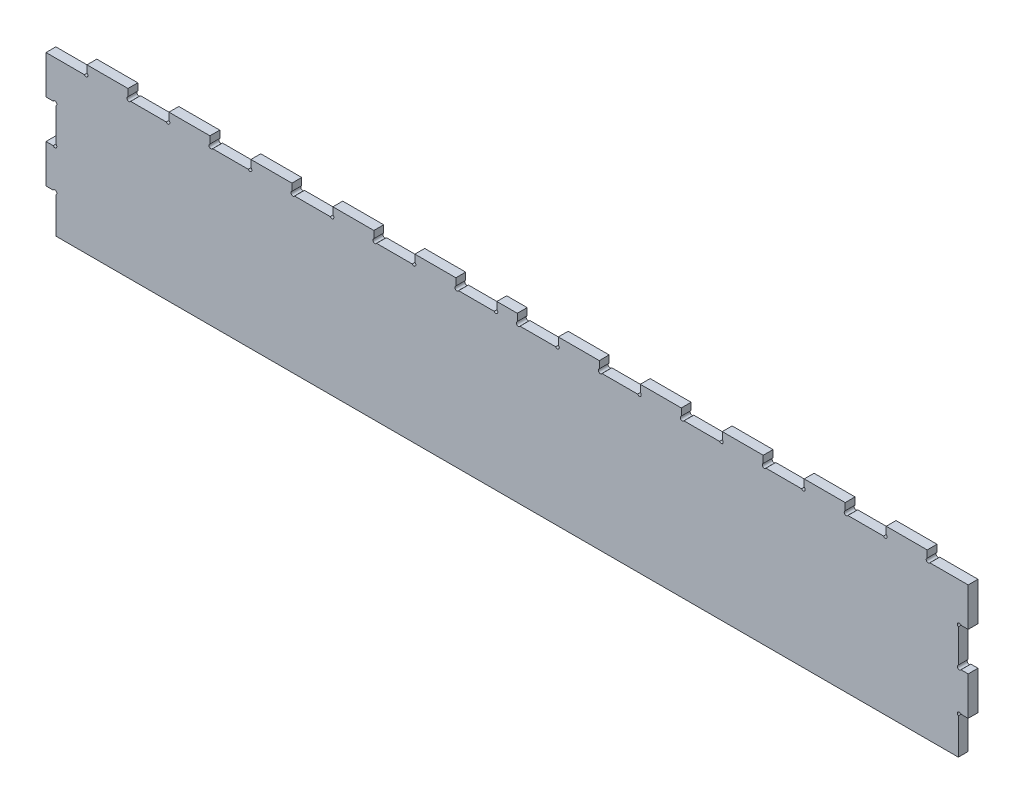
SolidWorks part; units mm, degrees
ref_plane "Front Plane" through (0, 0, 0) normal (0, 0, 1) x (1, 0, 0)
ref_plane "Top Plane" through (0, 0, 0) normal (0, 1, 0) x (1, 0, 0)
ref_plane "Right Plane" through (0, 0, 0) normal (1, 0, 0) x (0, 0, -1)
sketch "Sketch1" plane through (0, 0, 0) normal (0, 0, 1) x (1, 0, 0)
  line L0 (-398.4815, 104.8969) -> (-351.7791, 104.8969)
  line L1 (-348.4815, 116.8969) -> (-298.4815, 116.8969)
  line L2 (-398.4815, 104.8969) -> (-398.4815, 57.8969)
  line L3 (-386.4815, -83.1031) -> (714.5185, -83.1031)
  line L4 (726.5185, 104.8969) -> (726.5185, 57.8969)
  line L5 (-348.4815, 108.1642) -> (-348.4815, 116.8969)
  line L6 (-298.4815, 116.8969) -> (-298.4815, 108.1642)
  line L7 (-295.1839, 104.8969) -> (-251.7791, 104.8969)
  line L8 (-248.4815, 108.1642) -> (-248.4815, 116.8969)
  line L9 (-248.4815, 116.8969) -> (-198.4815, 116.8969)
  line L10 (-198.4815, 116.8969) -> (-198.4815, 108.1642)
  line L11 (-195.1839, 104.8969) -> (-151.7791, 104.8969)
  line L12 (-148.4815, 108.1642) -> (-148.4815, 116.8969)
  line L13 (-148.4815, 116.8969) -> (-98.4815, 116.8969)
  line L14 (-98.4815, 116.8969) -> (-98.4815, 108.1642)
  line L15 (-95.1839, 104.8969) -> (-51.7791, 104.8969)
  line L16 (426.5185, 108.1642) -> (426.5185, 116.8969)
  line L17 (426.5185, 116.8969) -> (476.5185, 116.8969)
  line L18 (-348.4815, 104.8969) -> (-348.4815, 107.2969) construction
  line L19 (-348.4815, 107.2969) -> (-348.4815, 106.0969) construction
  line L20 (-348.4815, 104.8969) -> (-348.4815, 107.2969) construction
  line L21 (-348.4815, 107.2969) -> (-348.4815, 106.0969) construction
  line L22 (-348.4815, 106.0969) -> (-454.6532, 106.0969) construction
  line L23 (-454.6532, 106.0969) -> (-401.5674, 106.0969) construction
  line L24 (-348.4815, 112.5305) -> (-298.4815, 112.5305) construction
  line L25 (-348.4815, 104.8969) -> (-349.7007, 104.8969) construction
  line L26 (-350.9198, 104.8969) -> (-349.7007, 104.8969) construction
  line L27 (-349.7007, 104.8969) -> (-349.7007, 106.4267) construction
  line L28 (-350.8815, 104.8969) -> (-350.9198, 104.8969) construction
  line L29 (-298.4815, 112.5305) -> (-323.4815, 112.5305) construction
  line L30 (-323.4815, 112.5305) -> (-323.4815, 101.2566) construction
  line L31 (-298.4815, 112.5305) -> (-248.4815, 112.5305) construction
  line L32 (-248.4815, 112.5305) -> (-273.4815, 112.5305) construction
  line L33 (-273.4815, 112.5305) -> (-273.4815, 99.7895) construction
  line L34 (-248.4815, 113.8454) -> (-198.4815, 113.8454) construction
  line L35 (-198.4815, 113.8454) -> (-223.4815, 113.8454) construction
  line L36 (-223.4815, 113.8454) -> (-223.4815, 90.9782) construction
  line L37 (-198.4815, 112.5305) -> (-148.4815, 112.5305) construction
  line L38 (-148.4815, 112.5305) -> (-173.4815, 112.5305) construction
  line L39 (-173.4815, 112.5305) -> (-173.4815, 98.0011) construction
  line L40 (-148.4815, 109.9027) -> (-98.4815, 109.9027) construction
  line L41 (-98.4815, 109.9027) -> (-123.4815, 109.9027) construction
  line L42 (-123.4815, 109.9027) -> (-123.4815, 98.0011) construction
  line L43 (651.5185, 116.8969) -> (651.5185, -83.1031) construction
  line L44 (651.5185, -83.1031) -> (651.5185, 16.8969) construction
  line L45 (164.0185, 10.8969) -> (164.0185, 307.3359) construction
  line L46 (426.5185, 116.8969) -> (426.5185, 108.1642)
  line L47 (476.5185, 108.1642) -> (476.5185, 116.8969)
  line L48 (523.2209, 104.8969) -> (479.8161, 104.8969)
  line L49 (526.5185, 116.8969) -> (526.5185, 108.1642)
  line L50 (576.5185, 108.1642) -> (576.5185, 116.8969)
  line L51 (623.2209, 104.8969) -> (579.8161, 104.8969)
  line L52 (626.5185, 116.8969) -> (626.5185, 108.1642)
  line L53 (676.5185, 108.1642) -> (676.5185, 116.8969)
  line L54 (726.5185, 104.8969) -> (679.8161, 104.8969)
  line L55 (526.5185, 116.8969) -> (576.5185, 116.8969)
  line L56 (626.5185, 116.8969) -> (676.5185, 116.8969)
  line L57 (651.5185, 16.8969) -> (-398.4815, 16.8969) construction
  line L58 (726.5185, 10.8969) -> (726.5185, -36.1031)
  line L59 (-388.8815, 57.8969) -> (-388.8748, 57.8969)
  line L60 (-386.4815, 57.8969) -> (-388.8748, 57.8969) construction
  line L61 (-388.8748, 57.8969) -> (-387.6782, 57.8969) construction
  line L62 (-387.6782, 57.8969) -> (-387.6782, 56.1544) construction
  line L63 (-386.4815, 57.8969) -> (-386.4815, 55.4969) construction
  line L64 (-386.4815, 55.4969) -> (-386.4815, 56.6969) construction
  line L65 (-386.4815, 56.6969) -> (-387.892, 56.6969) construction
  line L66 (-386.4815, 54.6165) -> (-386.4815, 14.1773)
  line L67 (714.5185, -71.1031) -> (714.5185, -83.1031)
  line L68 (714.5185, -39.3835) -> (714.5185, -71.1031)
  line L69 (726.5185, -36.1031) -> (717.7936, -36.1031)
  line L70 (717.7936, 10.8969) -> (726.5185, 10.8969)
  line L71 (714.5185, 54.6165) -> (714.5185, 14.1773)
  line L72 (726.5185, 57.8969) -> (717.7936, 57.8969)
  line L73 (-386.4815, -39.3835) -> (-386.4815, -83.1031)
  line L74 (376.5185, 108.1642) -> (376.5185, 116.8969)
  line L75 (376.5185, 116.8969) -> (326.5185, 116.8969)
  line L76 (326.5185, 116.8969) -> (326.5185, 108.1642)
  line L77 (379.8161, 104.8969) -> (423.2209, 104.8969)
  line L78 (276.5185, 108.1642) -> (276.5185, 116.8969)
  line L79 (276.5185, 116.8969) -> (226.5185, 116.8969)
  line L80 (226.5185, 116.8969) -> (226.5185, 108.1642)
  line L81 (279.8161, 104.8969) -> (323.2209, 104.8969)
  line L82 (176.5185, 108.1642) -> (176.5185, 116.8969)
  line L83 (-398.4815, 57.8969) -> (-389.7566, 57.8969)
  line L84 (-398.4815, 57.8969) -> (-398.4815, 10.8969) construction
  line L85 (-389.7566, 10.8969) -> (-398.4815, 10.8969)
  line L86 (-398.4815, 10.8969) -> (-398.4815, -36.1031)
  line L87 (-398.4815, -36.1031) -> (-389.7566, -36.1031)
  line L88 (176.5185, 116.8969) -> (151.5185, 116.8969)
  line L89 (151.5185, 116.8969) -> (151.5185, 108.1642)
  line L90 (179.8161, 104.8969) -> (223.2209, 104.8969)
  line L91 (376.5185, 116.8969) -> (426.5185, 116.8969) construction
  line L92 (-386.4815, 55.4969) -> (-386.4815, 57.8969) construction
  line L93 (351.5185, 116.8969) -> (351.5185, 66.1173) construction
  line L94 (301.5185, 104.8969) -> (301.5185, 57.8969) construction
  line L95 (-398.4815, 34.3969) -> (-378.9007, 34.3969) construction
  line L96 (-398.4815, -12.6031) -> (-375.299, -12.6031) construction
  line L97 (251.5185, 116.8969) -> (251.5185, 57.8969) construction
  line L98 (201.5185, 104.8969) -> (201.5185, 57.8969) construction
  line L99 (401.5185, 116.8969) -> (401.5185, 79.0498) construction
  line L100 (-48.4815, 108.1642) -> (-48.4815, 116.8969)
  line L101 (-48.4815, 116.8969) -> (1.5185, 116.8969)
  line L102 (51.5185, 116.8969) -> (101.5185, 116.8969)
  line L103 (1.5185, 116.8969) -> (1.5185, 108.1642)
  line L105 (51.5185, 108.1642) -> (51.5185, 116.8969)
  line L106 (101.5185, 116.8969) -> (101.5185, 108.1642)
  line L107 (104.8161, 104.8969) -> (148.2209, 104.8969)
  line L108 (4.8161, 104.8969) -> (48.2209, 104.8969)
  circle A0 centre (-348.4815, 104.8969) radius 2.4 construction
  arc A1 (-351.7791, 104.8969) -> (-348.4815, 108.1642) centre (-349.7007, 106.0969) ccw
  arc A2 (-295.1839, 104.8969) -> (-298.4815, 108.1642) centre (-297.2624, 106.0969) cw
  arc A3 (-251.7791, 104.8969) -> (-248.4815, 108.1642) centre (-249.7007, 106.0969) ccw
  arc A4 (-195.1839, 104.8969) -> (-198.4815, 108.1642) centre (-197.2624, 106.0969) cw
  arc A5 (-151.7791, 104.8969) -> (-148.4815, 108.1642) centre (-149.7007, 106.0969) ccw
  arc A6 (-95.1839, 104.8969) -> (-98.4815, 108.1642) centre (-97.2624, 106.0969) cw
  arc A7 (423.2209, 104.8969) -> (426.5185, 108.1642) centre (425.2993, 106.0969) ccw
  arc A8 (479.8161, 104.8969) -> (476.5185, 108.1642) centre (477.7376, 106.0969) cw
  arc A9 (523.2209, 104.8969) -> (526.5185, 108.1642) centre (525.2993, 106.0969) ccw
  arc A10 (579.8161, 104.8969) -> (576.5185, 108.1642) centre (577.7376, 106.0969) cw
  arc A11 (623.2209, 104.8969) -> (626.5185, 108.1642) centre (625.2993, 106.0969) ccw
  arc A12 (679.8161, 104.8969) -> (676.5185, 108.1642) centre (677.7376, 106.0969) cw
  circle A13 centre (-386.4815, 57.8969) radius 2.4 construction
  arc A14 (-386.4815, 54.6165) -> (-389.7566, 57.8969) centre (-387.6782, 56.6969) ccw
  arc A15 (-386.4815, 14.1773) -> (-389.7566, 10.8969) centre (-387.6782, 12.0969) cw
  arc A16 (-386.4815, -39.3835) -> (-389.7566, -36.1031) centre (-387.6782, -37.3031) ccw
  arc A17 (714.5185, -39.3835) -> (717.7936, -36.1031) centre (715.7151, -37.3031) cw
  arc A18 (714.5185, 14.1773) -> (717.7936, 10.8969) centre (715.7151, 12.0969) ccw
  arc A19 (714.5185, 54.6165) -> (717.7936, 57.8969) centre (715.7151, 56.6969) cw
  arc A20 (379.8161, 104.8969) -> (376.5185, 108.1642) centre (377.7376, 106.0969) cw
  arc A21 (323.2209, 104.8969) -> (326.5185, 108.1642) centre (325.2993, 106.0969) ccw
  arc A22 (279.8161, 104.8969) -> (276.5185, 108.1642) centre (277.7376, 106.0969) cw
  arc A23 (223.2209, 104.8969) -> (226.5185, 108.1642) centre (225.2993, 106.0969) ccw
  arc A24 (179.8161, 104.8969) -> (176.5185, 108.1642) centre (177.7376, 106.0969) cw
  arc A25 (148.2209, 104.8969) -> (151.5185, 108.1642) centre (150.2993, 106.0969) ccw
  arc A26 (-51.7791, 104.8969) -> (-48.4815, 108.1642) centre (-49.7007, 106.0969) ccw
  arc A27 (4.8161, 104.8969) -> (1.5185, 108.1642) centre (2.7376, 106.0969) cw
  arc A28 (48.2209, 104.8969) -> (51.5185, 108.1642) centre (50.2993, 106.0969) ccw
  arc A29 (104.8161, 104.8969) -> (101.5185, 108.1642) centre (102.7376, 106.0969) cw
  dimension "D10" = 4.8
  dimension "D11" = 4.8
  dimension "D13" = 4.8
  dimension "D14" = 4.8
  dimension "D1" = 50
  dimension "D2" = 47
  dimension "D3" = 50
  dimension "D4" = 12
  dimension "D5" = 188
  dimension "D6" = 50
  dimension "D7" = 47
  dimension "D8" = 50
  dimension "D9" = 12
  dimension "D12" = 47
  dimension "D15" = 50
  dimension "D16" = 1101
  dimension "D17" = 12
  dimension "D18" = 50
  dimension "D19" = 50
  dimension "D21" = 50
  dimension "D22" = 50
  dimension "D23" = 50
  dimension "D24" = 25
extrude "Boss-Extrude1" add sketch "Sketch1" along normal blind 12 contours L17 L47 A8 L48 A9 L49 L55 L50 A10 L51 A11 L52 L56 L53 A12 L54 L4 L72 A19 L71 A18 L70 L58 L69 A17 L68 L67 L3 L73 A16 L87 L86 L85 A15 L66 A14 L83 L2 L0 A1 L5 L1 L6 A2 L7 A3 L8 L9 L10 A4 L11 A5 L12 L13 L14 A6 L15 A26 L100 L101 L103 A27 L108 A28 L105 L102 L106 A29 L107 A25 L89 L88 L82 A24 L90 A23 L80 L79 L78 A22 L81 A21 L76 L75 L74 A20 L77 A7 L16
